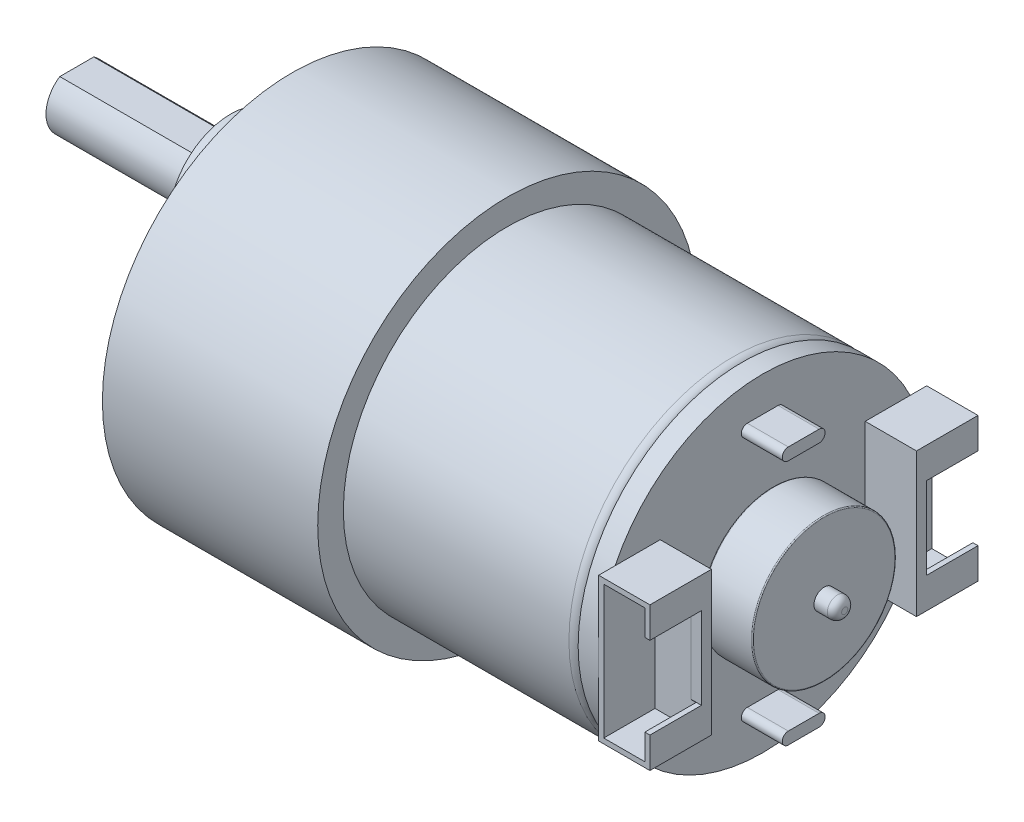
SolidWorks part; units mm, degrees
ref_plane "Front Plane" through (0, 0, 0) normal (0, 0, 1) x (1, 0, 0)
ref_plane "Top Plane" through (0, 0, 0) normal (0, 1, 0) x (1, 0, 0)
ref_plane "Right Plane" through (0, 0, 0) normal (1, 0, 0) x (0, 0, -1)
sketch "Sketch1" plane through (0, 0, 0) normal (0, 1, 0) x (1, 0, 0)
  line L0 (-69.831, 0) -> (81.9906, 0) construction
  line L1 (0, 38.4765) -> (0, -33.9601) construction
  line L2 (0, 18.5) -> (-21, 18.5)
  line L3 (-21, 18.5) -> (-21, 0)
  line L4 (0, 18.5) -> (0, 16)
  line L5 (0, 16) -> (22, 16)
  line L6 (22.9, 15.1) -> (22.9, 1)
  line L7 (22.9, 1) -> (32.2, 1)
  line L8 (32.9, 0.3) -> (32.9, 0)
  line L9 (-21, 0) -> (32.9, 0)
  arc A0 (22, 16) -> (22.9, 15.1) centre (22, 15.1) cw
  arc A1 (32.2, 1) -> (32.9, 0.3) centre (32.2, 0.3) cw
  point P13 (22.9, 16)
  point P19 (32.9, 1)
  dimension "D3" = 0.9
  dimension "D8" = 0.7
  dimension "D1" = 18.5
  dimension "D4" = 21
  dimension "D5" = 22
  dimension "D6" = 1
  dimension "D7" = 10
revolve "Revolve1" add sketch "Sketch1" angle 360 about L9
sketch "Sketch2" plane through (-21, 0, 0) normal (-1, 0, 0) x (0, 0, 1)
  circle A0 centre (0, 6) radius 6
  dimension "D2" = 12
  dimension "D1" = 6
extrude "Boss-Extrude1" add sketch "Sketch2" along normal blind 6
sketch "Sketch3" plane through (-27, 0, 0) normal (-1, 0, 0) x (0, 0, 1)
  circle A2 centre (0, 6) radius 3
  dimension "D1" = 6
extrude "Boss-Extrude2" add sketch "Sketch3" along normal blind 15
sketch "Sketch4" plane through (-42, 0, 0) normal (-1, 0, 0) x (0, 0, 1)
  line L0 (-1.6583, 8.5) -> (1.6583, 8.5)
  circle A0 centre (0, 6) radius 3 construction
  arc A1 (1.6583, 8.5) -> (-1.6583, 8.5) centre (0, 6) ccw
  point P3 (0, 8.5)
  dimension "D1" = 2.5
extrude "Cut-Extrude1" cut sketch "Sketch4" against normal blind 13
sketch "Sketch5" plane through (-21, 0, 0) normal (-1, 0, 0) x (0, 0, 1)
  arc A0 (-4.9826, 10.9167) -> (4.9826, 10.9167) centre (0, 6) ccw
  arc A1 (-4.9826, 10.9167) -> (4.9826, 10.9167) centre (0, 0) ccw
  point P0 (0, 6)
  dimension "D1" = 14
  dimension "D2" = 24
extrude "Cut-Extrude2" cut sketch "Sketch5" against normal blind 0.5
sketch "Sketch6" plane through (-21, 0, 0) normal (-1, 0, 0) x (0, 0, 1)
  line L0 (-24.2298, 0) -> (26.5129, 0) construction
  line L1 (0, 19.7742) -> (0, -20.8789) construction
  circle A0 centre (15, 0) radius 1.5
  arc A1 (-4.9826, 10.9167) -> (4.9826, 10.9167) centre (0, 0) ccw construction
  dimension "D2" = 3
  dimension "D1" = 15
extrude "Cut-Extrude3" cut sketch "Sketch6" against normal blind 2
pattern_circular "CirPattern1" count 6 over 360 about axis through (0, 0, 0) along (1, 0, 0) of "Cut-Extrude3"
sketch "Sketch7" plane through (22.9, 0, 0) normal (1, 0, 0) x (0, 0, -1)
  line L0 (0, 26.5129) -> (0, -36.6025) construction
  line L1 (19.9215, 0) -> (-21.1735, 0) construction
  line L2 (1.5, 12) -> (-1.5, 12) construction
  line L3 (1.5, 11.4108) -> (-1.5, 11.4108)
  line L4 (1.5, 12.5892) -> (-1.5, 12.5892)
  line L5 (1.5, -12) -> (-1.5, -12) construction
  line L6 (1.5, -11.4108) -> (-1.5, -11.4108)
  line L7 (1.5, -12.5892) -> (-1.5, -12.5892)
  arc A0 (1.5, 11.4108) -> (1.5, 12.5892) centre (1.5, 12) ccw
  arc A1 (-1.5, 12.5892) -> (-1.5, 11.4108) centre (-1.5, 12) ccw
  arc A4 (1.5, -11.4108) -> (1.5, -12.5892) centre (1.5, -12) cw
  arc A5 (-1.5, -12.5892) -> (-1.5, -11.4108) centre (-1.5, -12) cw
  point P7 (0, 12)
  point P17 (0, -12)
  dimension "D1" = 3
extrude "Boss-Extrude3" add sketch "Sketch7" along normal blind 6
sketch "Sketch8" plane through (22.9, 0, 0) normal (1, 0, 0) x (0, 0, -1)
  circle A0 centre (0, 0) radius 16
  dimension "D1" = 32
extrude "Boss-Extrude4" add sketch "Sketch8" along normal blind 2
sketch "Sketch9" plane through (24.9, 0, 0) normal (1, 0, 0) x (0, 0, -1)
  circle A0 centre (0, 0) radius 7
  dimension "D1" = 14
extrude "Boss-Extrude5" add sketch "Sketch9" along normal blind 6
sketch "Sketch10" plane through (24.9, 0, 0) normal (1, 0, 0) x (0, 0, -1)
  circle A0 centre (0, 0) radius 7
  circle A1 centre (0, 0) radius 1
  dimension "D1" = 2
  dimension "D2" = 14
extrude "Cut-Extrude4" cut sketch "Sketch10" along normal blind 1
fillet "Fillet2" radius 0.1 1 edges at (30.9, 0, -7)
fillet "Fillet3" radius 0.1 1 edges at (25.9, 0, -7)
sketch "Sketch11" plane through (24.9, 0, 0) normal (1, 0, 0) x (0, 0, -1)
  line L0 (10, 7) -> (10, -7)
  line L1 (10, 7) -> (16, 7)
  line L2 (16, 7) -> (16, -7)
  line L3 (16, -7) -> (10, -7)
  circle A0 centre (0, 0) radius 0.3 construction
  point P0 (10, 0)
  dimension "D1" = 10
  dimension "D2" = 14
  dimension "D3" = 6
extrude "Boss-Extrude6" add sketch "Sketch11" along normal blind 5
sketch "Sketch13" plane through (0, 0, -16) normal (0, 0, -1) x (-1, 0, 0)
  line L0 (-29.4, 6.5) -> (-29.4, -6.5)
  line L2 (-25.4, 6.5) -> (-25.4, -6.5)
  line L3 (-29.4, 6.5) -> (-25.4, 6.5)
  line L4 (-29.9, 7) -> (-24.9, 7) construction
  line L5 (-25.4, -6.5) -> (-29.4, -6.5)
  line L6 (-29.9, -7) -> (-29.9, 7) construction
  dimension "D1" = 13
  dimension "D2" = 4
  dimension "D3" = 0.5
  dimension "D4" = 0.5
extrude "Cut-Extrude6" cut sketch "Sketch13" against normal blind 5
sketch "Sketch14" plane through (29.9, 0, 0) normal (1, 0, 0) x (0, 0, -1)
  line L0 (16, 4) -> (10.9734, 4)
  line L1 (16, -7) -> (16, 7) construction
  line L2 (10.9734, 4) -> (10.9734, -4)
  line L3 (16, 4) -> (16, -4)
  line L4 (23.2724, 0) -> (-21.284, 0) construction
  line L5 (16, -4) -> (10.9734, -4)
  point P10 (16, 0)
  point P11 (10.9734, 0)
  dimension "D1" = 4
extrude "Cut-Extrude7" cut sketch "Sketch14" against normal blind 1
mirror "Mirror1" about plane through (0, 0, 0) normal (0, 0, 1) of "Cut-Extrude7", "Cut-Extrude6", "Boss-Extrude6"
